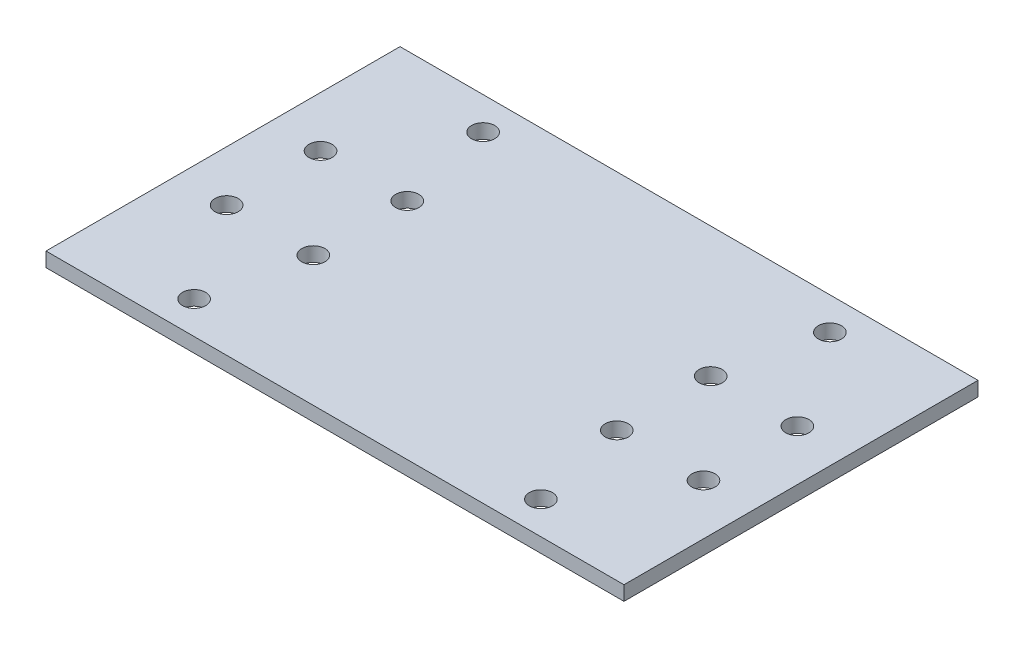
SolidWorks part; units mm, degrees
ref_plane "前基準面" through (0, 0, 0) normal (0, 0, 1) x (1, 0, 0)
ref_plane "上基準面" through (0, 0, 0) normal (0, 1, 0) x (1, 0, 0)
ref_plane "右基準面" through (0, 0, 0) normal (1, 0, 0) x (0, 0, -1)
sketch "草圖1" plane through (0, 0, 0) normal (0, 1, 0) x (1, 0, 0)
  line L1 (-40, -24.5) -> (40, -24.5)
  line L2 (-40, -24.5) -> (-40, 24.5)
  line L3 (-40, 24.5) -> (40, 24.5)
  line L4 (40, -24.5) -> (40, 24.5)
  line L5 (0, 24.5) -> (0, -24.5) construction
  line L6 (-40, 0) -> (40, 0) construction
  circle A0 centre (-33, 6.5) radius 1.6
  circle A1 centre (33, 6.5) radius 1.6
  circle A2 centre (33, -6.5) radius 1.6
  circle A3 centre (-33, -6.5) radius 1.6
  circle A4 centre (-21, 6.5) radius 1.6
  circle A5 centre (21, 6.5) radius 1.6
  circle A6 centre (-21, -6.5) radius 1.6
  circle A7 centre (21, -6.5) radius 1.6
  circle A8 centre (-24, -20) radius 1.6
  circle A9 centre (24, -20) radius 1.6
  circle A10 centre (24, 20) radius 1.6
  circle A11 centre (-24, 20) radius 1.6
  point P0 (0, 0)
  point P36 (0, 0)
  point P37 (0, 0)
  point P38 (-32.0124, 28.9332)
  dimension "D4" = 3.2
  dimension "D1" = 13
  dimension "D2" = 12
  dimension "D3" = 54
  dimension "D5" = 49
  dimension "D6" = 80
  dimension "D7" = 48
  dimension "D9" = 40
extrude "填料-伸長1" add sketch "草圖1" along normal blind 2
